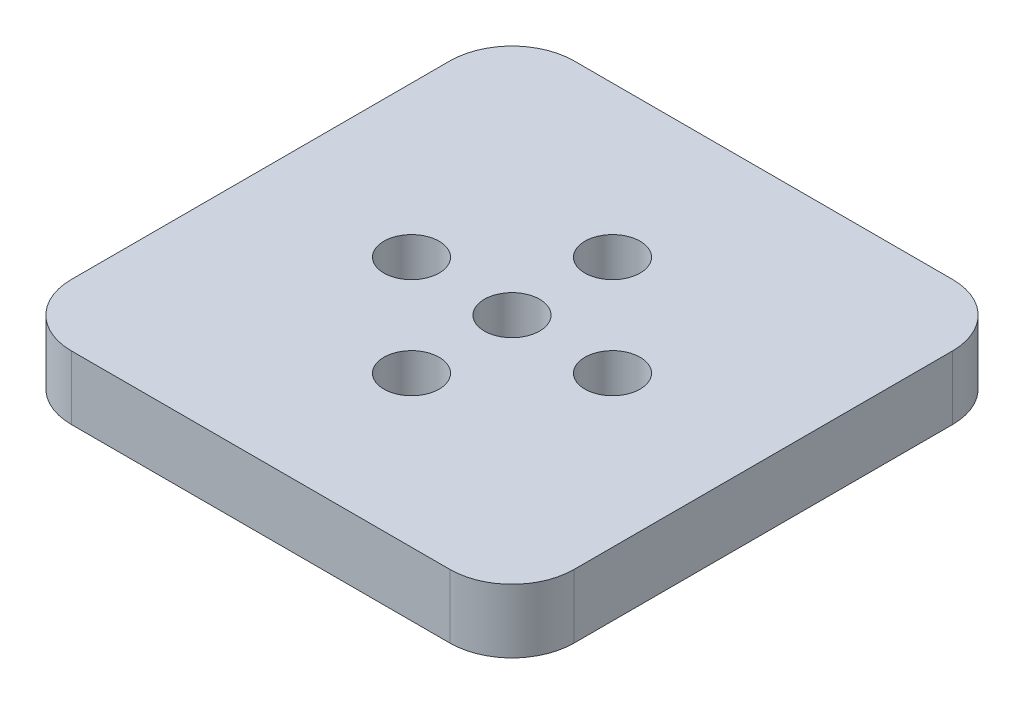
SolidWorks part; units mm, degrees
ref_plane "정면" through (0, 0, 0) normal (0, 0, 1) x (1, 0, 0)
ref_plane "윗면" through (0, 0, 0) normal (0, 1, 0) x (1, 0, 0)
ref_plane "우측면" through (0, 0, 0) normal (1, 0, 0) x (0, 0, -1)
sketch "스케치1" plane through (0, 0, 0) normal (0, 1, 0) x (1, 0, 0)
  line L1 (-18.83, 25) -> (18.83, 25)
  line L2 (-25, 18.83) -> (-25, -18.83)
  line L3 (-18.83, -25) -> (18.83, -25)
  line L4 (25, 18.83) -> (25, -18.83)
  line L5 (-25, 25) -> (25, -25) construction
  line L6 (-25, -25) -> (25, 25) construction
  arc A0 (18.83, 25) -> (25, 18.83) centre (18.83, 18.83) cw
  arc A1 (25, -18.83) -> (18.83, -25) centre (18.83, -18.83) cw
  arc A2 (-18.83, -25) -> (-25, -18.83) centre (-18.83, -18.83) cw
  arc A3 (-25, 18.83) -> (-18.83, 25) centre (-18.83, 18.83) cw
  point P4 (0, 0)
  point P5 (0, 10)
  point P8 (0, 0)
  point P11 (10, 0)
  point P12 (0, -10)
  point P13 (-10, 0)
  point P14 (0, 0)
  dimension "D5" = 6.17
  dimension "D1" = 50
  dimension "D2" = 50
  dimension "D3" = 10
  dimension "D4" = 4
extrude "보스-돌출1" add sketch "스케치1" against normal blind 6.35
hole_wizard "M5 여유 구멍1" positions "스케치2" profile "스케치3" hole size "M5" standard "KS" end condition through all
sketch "스케치2" plane through (0, 0, 0) normal (0, 1, 0) x (1, 0, 0)
  point P0 (0, 10)
  point P3 (10, 0)
  point P6 (0, -10)
  point P9 (-10, 0)
  point P12 (0, 0)
sketch "스케치3" plane through (0, 0, -10) normal (1, 0, 0) x (0, 0, 1)
  line L0 (0, 0) -> (0, 6.35)
  line L1 (0, 6.35) -> (2.75, 6.35)
  line L2 (2.75, 6.35) -> (2.75, 0)
  line L5 (2.75, 0) -> (0, 0)
  line L11 (0, -6.35) -> (0, 107.95) construction
  dimension "관통 구멍 지름" = 5.5
  dimension "관통 구멍 깊이" = 6.35
sketch "스케치4" plane through (0, 0, 25) normal (0, 0, 1) x (1, 0, 0)
  line L0 (-21.2, -6.35) -> (-21.2, -13.1)
  line L1 (-21.2, -13.1) -> (-23.9, -13.1)
  line L2 (-23.9, -13.1) -> (-23.9, -22.1)
  line L3 (-23.9, -22.1) -> (-20.6, -22.1)
  line L4 (-20.6, -22.1) -> (-20.6, -26.9)
  line L5 (-20.6, -26.9) -> (-11.8, -26.9)
  line L6 (-11.8, -26.9) -> (-11.8, -22.1)
  line L7 (-11.8, -22.1) -> (-8.5, -22.1)
  line L8 (-8.5, -22.1) -> (-8.5, -13.1)
  line L9 (-8.5, -13.1) -> (-11.2, -13.1)
  line L10 (-11.2, -13.1) -> (-11.2, -6.35)
  line L11 (-18.83, -6.35) -> (18.83, -6.35) construction
  line L12 (-25, -6.35) -> (-25, 0) construction
  line L14 (0, -14.795) -> (0, 14.795) construction
  line L15 (11.2, -13.1) -> (11.2, -6.35)
  line L16 (8.5, -13.1) -> (11.2, -13.1)
  line L17 (8.5, -22.1) -> (8.5, -13.1)
  line L18 (11.8, -22.1) -> (8.5, -22.1)
  line L19 (11.8, -26.9) -> (11.8, -22.1)
  line L20 (20.6, -26.9) -> (11.8, -26.9)
  line L21 (20.6, -22.1) -> (20.6, -26.9)
  line L22 (23.9, -22.1) -> (20.6, -22.1)
  line L23 (23.9, -13.1) -> (23.9, -22.1)
  line L24 (21.2, -13.1) -> (23.9, -13.1)
  line L25 (21.2, -6.35) -> (21.2, -13.1)
  point P14 (0, 0)
  point P15 (0, 0)
  point P16 (0, 0)
  point P17 (0, 0)
  dimension "D1" = 10
  dimension "D2" = 6.75
  dimension "D3" = 15.4
  dimension "D4" = 9
  dimension "D5" = 8.8
  dimension "D6" = 4.8
  dimension "D7" = 3.8
